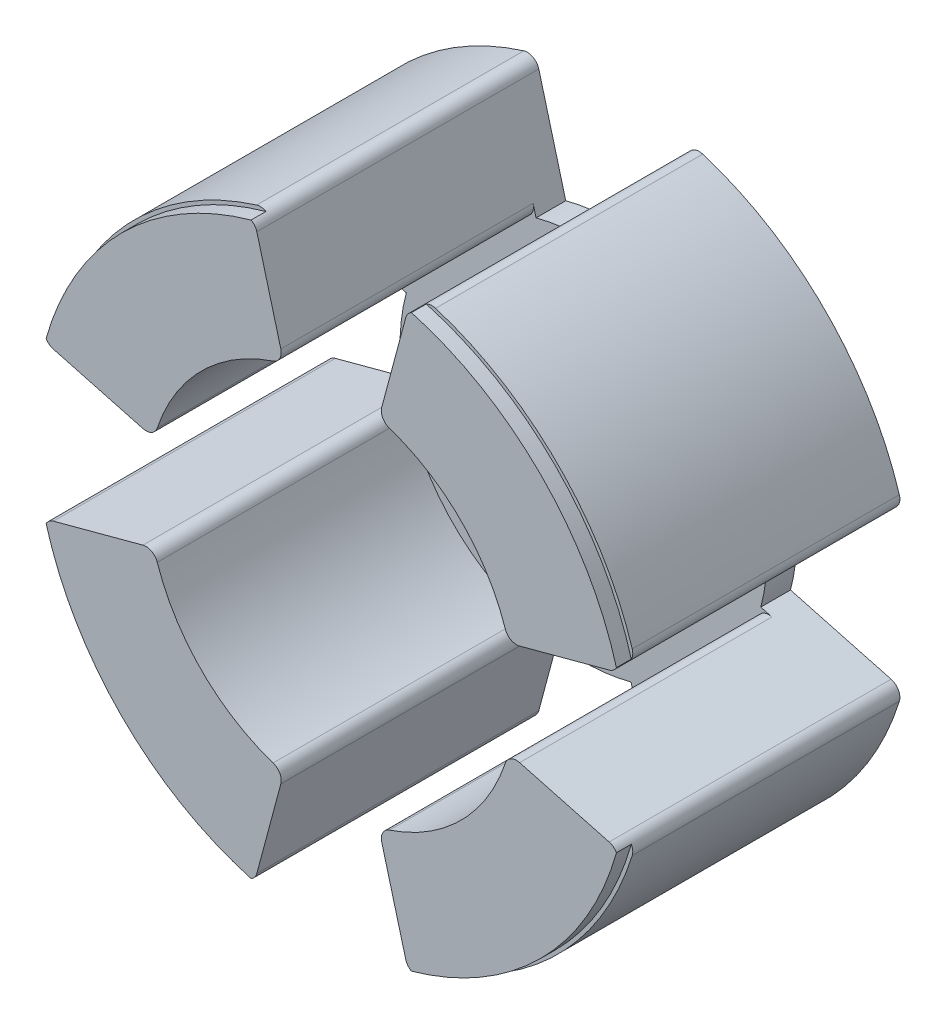
SolidWorks part; units mm, degrees
ref_plane "Front Plane" through (0, 0, 0) normal (0, 0, 1) x (1, 0, 0)
ref_plane "Top Plane" through (0, 0, 0) normal (0, 1, 0) x (1, 0, 0)
ref_plane "Right Plane" through (0, 0, 0) normal (1, 0, 0) x (0, 0, -1)
sketch "Sketch2" plane through (0, 0, 0) normal (0, 0, 1) x (1, 0, 0)
  circle A0 centre (0, 0) radius 64.135
  dimension "D1" = 128.27
extrude "Boss-Extrude1" add sketch "Sketch2" along normal blind 6.35
sketch "Sketch3" plane through (0, 0, 6.35) normal (0, 0, 1) x (1, 0, 0)
  circle A0 centre (0, 0) radius 39.2557
  circle A1 centre (0, 0) radius 64.135
  circle A2 centre (0, 0) radius 64.135
  dimension "D2" = 78.5114
  dimension "D1" = 0
extrude "Boss-Extrude2" add sketch "Sketch3" along normal blind 50.8
sketch "Sketch4" plane through (0, 0, 57.15) normal (0, 0, 1) x (1, 0, 0)
  circle A0 centre (0, 0) radius 39.2557 construction
  circle A1 centre (0, 0) radius 39.2557
  circle A2 centre (0, 0) radius 63.373
  dimension "D1" = 126.746
extrude "Boss-Extrude3" add sketch "Sketch4" along normal blind 3.175
sketch "Sketch5" plane through (0, 0, 60.325) normal (0, 0, 1) x (1, 0, 0)
  line L0 (-10.1601, 37.9181) -> (-16.5994, 61.9497)
  line L1 (10.1601, 37.9181) -> (16.5994, 61.9497)
  line L2 (0, -1000) -> (0, 49000) construction
  line L3 (0, 0) -> (-10.1601, 37.9181) construction
  line L4 (0, 0) -> (10.1601, 37.9181) construction
  circle A0 centre (0, 0) radius 64.135 construction
  arc A1 (16.5994, 61.9497) -> (-16.5994, 61.9497) centre (0, 0) ccw
  circle A2 centre (0, 0) radius 39.2557 construction
  arc A3 (10.1601, 37.9181) -> (-10.1601, 37.9181) centre (0, 0) ccw
  arc A4 (0, -64.135) -> (16.5994, 61.9497) centre (0, 0) ccw construction
  arc A5 (0, -39.2557) -> (10.1601, 37.9181) centre (0, 0) ccw construction
  arc A6 (-16.5994, 61.9497) -> (0, -64.135) centre (0, 0) ccw construction
  arc A7 (-10.1601, 37.9181) -> (0, -39.2557) centre (0, 0) ccw construction
  dimension "D1" = 15
  dimension "D2" = 15
extrude "Cut-Extrude1" cut sketch "Sketch5" against normal through all
fillet "Fillet1" radius 2.54 4 edges at (16.5994, 61.9497, 28.575) (10.1601, 37.9181, 33.3375) (-10.1601, 37.9181, 33.3375) (-16.5994, 61.9497, 28.575)
pattern_circular "CirPattern1" count 4 over 360 about axis through (0, 0, 0) along (0, 0, 1) of "Fillet1", "Cut-Extrude1"
equation "\"AIRFRAME_OD\"= 5.15in"
equation "\"AIRFRAME_ID\"= 4.99in"
equation "\"FLAT_T\"= 0.125in"
equation "\"COUPLER_OD\"= 4.998in"
equation "\"COUPLER_ID\"= 4.85in"
equation "\"NOSE_EXP_L\"= 27in"
equation "\"NOSE_SHOULDER_L\"= 5in"
equation "\"MAIN_L\"= 30in"
equation "\"RECO_COUP_L\"= 10in"
equation "\"RECO_SWITCH_L\"= 2in"
equation "\"RECO_ROD_X\"= 3.5in"
equation "\"DROGUE_L\"= 20in"
equation "\"ATS_FORE_COUP_L\"= 5.5in"
equation "\"ATS_AFT_COUP_L\"= 4.5in"
equation "\"ATS_ROD_X\"= 3.75in"
equation "\"LOWER_L\"= 30in"
equation "\"FIN_ROOT\"= 8in"
equation "\"FIN_X\"= 0.75in"
equation "\"FIN_N\"= 4"
equation "\"MOTOR_OD\"= 3.091in"
equation "\"MOTOR_ID\"= 3.00in"
equation "\"MOTOR_L\"= 14in"
equation "\"CR_AFT_X\"= 0.5in"
equation "\"CR_FORE_X\"= 9.25in"
equation "\"MOTOR_LOWER_X\"= 2in"
equation "\"D1@Sketch2\"=\"AIRFRAME_OD\"-0.1"
equation "\"D2@Sketch3\"=\"MOTOR_OD\""
equation "\"D1@Sketch4\"=\"AIRFRAME_ID\""
